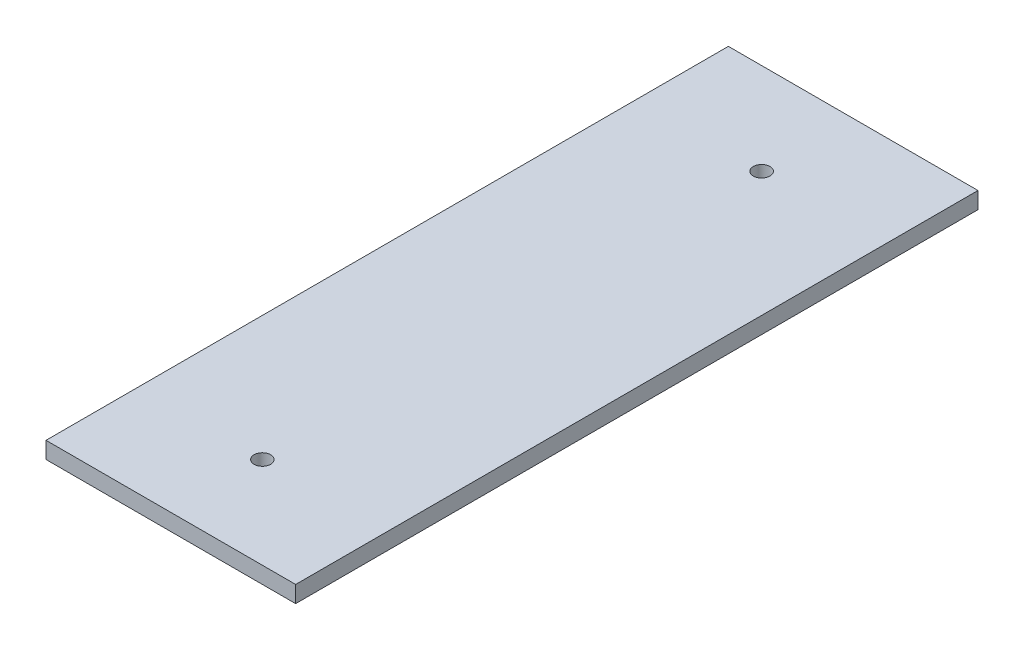
SolidWorks part; units mm, degrees
material "Liga 1060"
ref_plane "Plano frontal" through (0, 0, 0) normal (0, 0, 1) x (1, 0, 0)
ref_plane "Plano superior" through (0, 0, 0) normal (0, 1, 0) x (1, 0, 0)
ref_plane "Plano direito" through (0, 0, 0) normal (1, 0, 0) x (0, 0, -1)
sketch "Esboço1" plane through (0, 0, 0) normal (0, 1, 0) x (1, 0, 0)
  line L1 (0, 0) -> (30, 0)
  line L2 (0, 0) -> (0, 82)
  line L3 (0, 82) -> (30, 82)
  line L4 (30, 0) -> (30, 82)
  dimension "D1" = 82
  dimension "D2" = 30
extrude "Ressalto-extrusão1" add sketch "Esboço1" along normal blind 2
sketch "Esboço2" plane through (0, 2, 0) normal (0, 1, 0) x (1, 0, 0)
  line L0 (0, 41) -> (30, 41) construction
  line L1 (0, 82) -> (0, 0) construction
  line L2 (30, 0) -> (30, 82) construction
  circle A0 centre (15, 71) radius 1
  circle A1 centre (15, 11) radius 1
  dimension "D1" = 2
  dimension "D2" = 30
  dimension "D3" = 15
extrude "Corte-extrusão1" cut sketch "Esboço2" against normal through all
